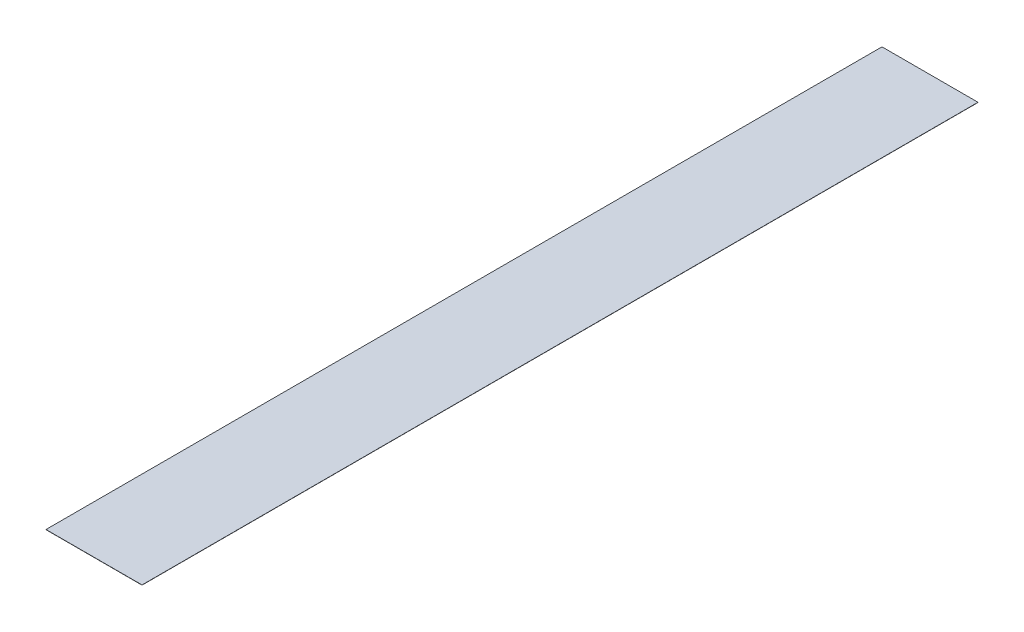
SolidWorks part; units mm, degrees
material "acrylic adhesive"
ref_plane "Front" through (0, 0, 0) normal (0, 0, 1) x (1, 0, 0)
ref_plane "Top" through (0, 0, 0) normal (0, 1, 0) x (1, 0, 0)
ref_plane "Right" through (0, 0, 0) normal (1, 0, 0) x (0, 0, -1)
sketch "Sketch1" plane through (0, 0, 0) normal (0, 1, 0) x (1, 0, 0)
  line L0 (-11.615, 101.995) -> (11.615, -101.995) construction
  line L1 (-11.615, 101.995) -> (11.615, 101.995)
  line L2 (-11.615, 101.995) -> (-11.615, -101.995)
  line L3 (-11.615, -101.995) -> (11.615, -101.995)
  line L4 (11.615, 101.995) -> (11.615, -101.995)
  point P4 (0, 0)
  dimension "D1" = 203.99
  dimension "D2" = 23.23
extrude "Extrude1" add sketch "Sketch1" along normal blind 0.0508
sketch "Sketch2" plane through (0, 0.0508, 0) normal (0, 1, 0) x (1, 0, 0)
  line L0 (-11.615, -101.995) -> (-11.615, 101.995)
  line L1 (-11.615, -101.995) -> (-11.815, -101.995)
  line L2 (-11.615, 101.995) -> (-11.815, 101.995)
  line L3 (-11.815, -101.995) -> (-11.815, 101.995)
  dimension "D1" = 0.2
extrude "Boss-Extrude1" add sketch "Sketch2" against normal through all
